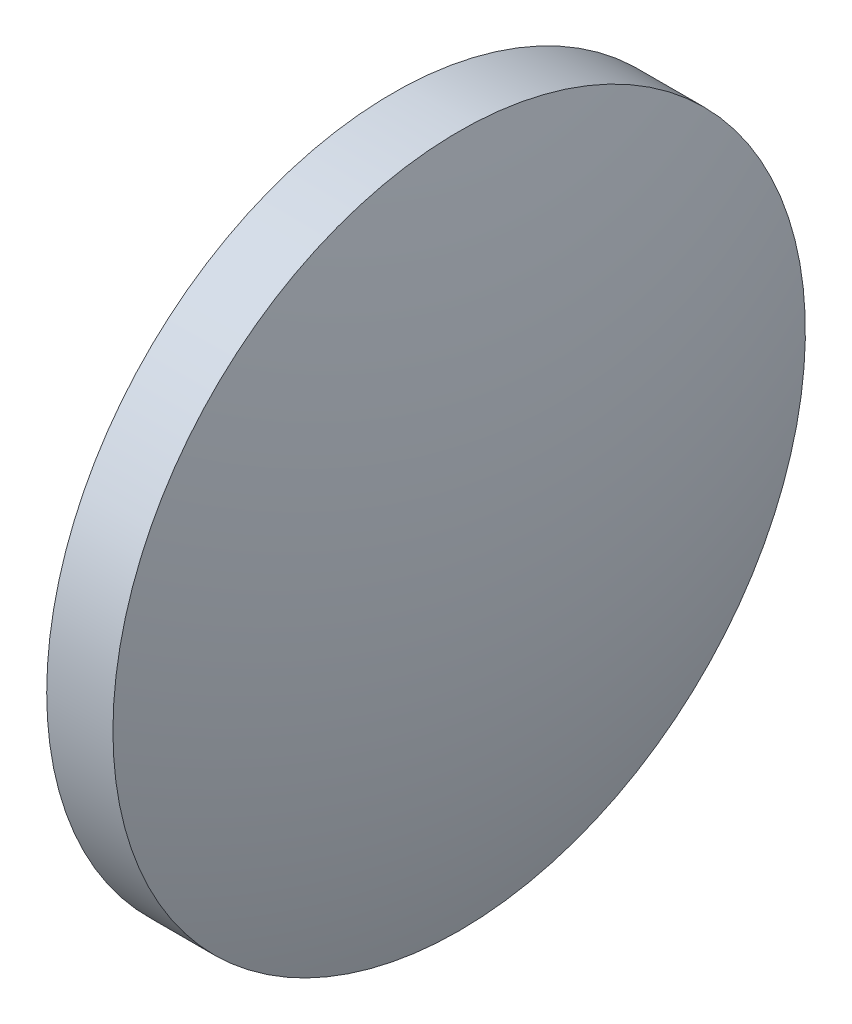
SolidWorks part; units mm, degrees
ref_plane "前视基准面" through (0, 0, 0) normal (0, 0, 1) x (1, 0, 0)
ref_plane "上视基准面" through (0, 0, 0) normal (0, 1, 0) x (1, 0, 0)
ref_plane "右视基准面" through (0, 0, 0) normal (1, 0, 0) x (0, 0, -1)
sketch "草图1" plane through (0, 0, 0) normal (0, 0, 1) x (1, 0, 0)
  line L0 (500.8301, 80.1995) -> (510.4259, 80.1995) construction
  line L1 (502.4781, 80.1995) -> (502.4781, 88.1995)
  line L2 (505.2781, 80.1995) -> (502.4781, 80.1995)
  line L5 (502.4781, 88.1995) -> (504.0081, 88.1995)
  arc A0 (505.2781, 80.1995) -> (504.0081, 88.1995) centre (479.4462, 80.1995) ccw
revolve "旋转1" add sketch "草图1" angle 360 about L0
